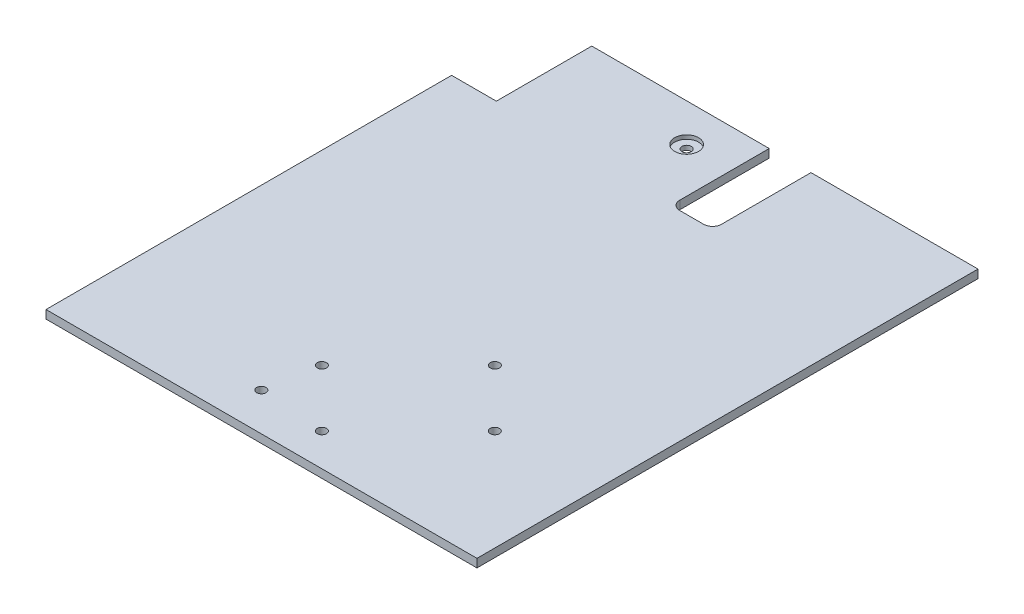
SolidWorks part; units mm, degrees
ref_plane "Front" through (0, 0, 0) normal (0, 0, 1) x (1, 0, 0)
ref_plane "Top" through (0, 0, 0) normal (0, 1, 0) x (1, 0, 0)
ref_plane "Right" through (0, 0, 0) normal (1, 0, 0) x (0, 0, -1)
sketch "Sketch1" plane through (0, 0, 0) normal (0, 1, 0) x (1, 0, 0)
  line L0 (-9.7916, -53.9497) -> (19.1997, -24.9584) construction
  line L1 (-72.25, -84) -> (72.25, -84)
  line L2 (-72.25, -84) -> (-72.25, 84)
  line L3 (-72.25, 84) -> (72.25, 84)
  line L4 (72.25, -84) -> (72.25, 84)
  line L5 (-72.25, -84) -> (72.25, 84) construction
  line L6 (-72.25, 84) -> (72.25, -84) construction
  line L7 (-72.25, 84) -> (-57.25, 84)
  line L8 (-72.25, 84) -> (-72.25, 52)
  line L9 (-72.25, 52) -> (-57.25, 52)
  line L10 (-57.25, 84) -> (-57.25, 52)
  line L11 (-72.25, 84) -> (-57.25, 52) construction
  line L12 (-72.25, 52) -> (-57.25, 84) construction
  line L13 (-9.7916, -53.9497) -> (9.3003, -73.0416) construction
  line L14 (19.1997, -24.9584) -> (38.2916, -44.0503) construction
  line L15 (9.3003, -73.0416) -> (38.2916, -44.0503) construction
  line L16 (-9.7916, -53.9497) -> (38.2916, -44.0503) construction
  circle A0 centre (19.1997, -24.9584) radius 1.55
  circle A1 centre (38.2916, -44.0503) radius 1.55
  circle A2 centre (-9.7916, -53.9497) radius 1.55
  circle A3 centre (9.3003, -73.0416) radius 1.55
  point P0 (0, 0)
  point P9 (-64.75, 68)
  point P10 (14.25, -49)
  dimension "D10" = 3.1
  dimension "D11" = 3.1
  dimension "D12" = 3.1
  dimension "D13" = 3.1
  dimension "D1" = 168
  dimension "D2" = 144.5
  dimension "D3" = 32
  dimension "D4" = 15
  dimension "D5" = 41
  dimension "D6" = 27
  dimension "D7" = 45
  dimension "D8" = 58
  dimension "D9" = 35
extrude "Boss-Extrude1" add sketch "Sketch1" along normal blind 2.8 contours L3 L10 L9 L2 L1 L4 A3 A2 A1 A0
sketch "Sketch2" plane through (0, 2.8, 0) normal (0, 1, 0) x (1, 0, 0)
  line L0 (-57.25, 84) -> (72.25, 84) construction
  line L1 (72.25, -84) -> (72.25, 84) construction
  line L2 (-72.25, -84) -> (72.25, -84) construction
  circle A0 centre (-12.75, 71.3) radius 1.55
  circle A1 centre (-12.75, -71.3) radius 1.55
  dimension "D1" = 3.1
  dimension "D2" = 3.1
  dimension "D4" = 85
  dimension "D5" = 12.7
  dimension "D3" = 12.7
extrude "Cut-Extrude1" cut sketch "Sketch2" against normal up to next
sketch "Sketch3" plane through (0, 2.8, 0) normal (0, 1, 0) x (1, 0, 0)
  circle A0 centre (-12.75, 71.3) radius 4
  dimension "D1" = 8
extrude "Cut-Extrude2" cut sketch "Sketch3" against normal blind 1.3
sketch "Sketch4" plane through (0, 2.8, 0) normal (0, 1, 0) x (1, 0, 0)
  line L0 (-57.25, 84) -> (72.25, 84) construction
  line L1 (16.25, 84) -> (2.25, 84)
  line L2 (16.25, 84) -> (16.25, 54)
  line L3 (13.25, 51) -> (5.25, 51)
  line L4 (2.25, 84) -> (2.25, 54)
  line L5 (16.25, 84) -> (2.25, 51) construction
  line L6 (16.25, 51) -> (2.25, 84) construction
  line L7 (72.25, -84) -> (72.25, 84) construction
  arc A0 (16.25, 54) -> (13.25, 51) centre (13.25, 54) cw
  arc A1 (2.25, 54) -> (5.25, 51) centre (5.25, 54) ccw
  point P4 (9.25, 67.5)
  dimension "D4" = 3
  dimension "D1" = 56
  dimension "D2" = 14
  dimension "D3" = 33
extrude "Cut-Extrude3" cut sketch "Sketch4" against normal up to next
